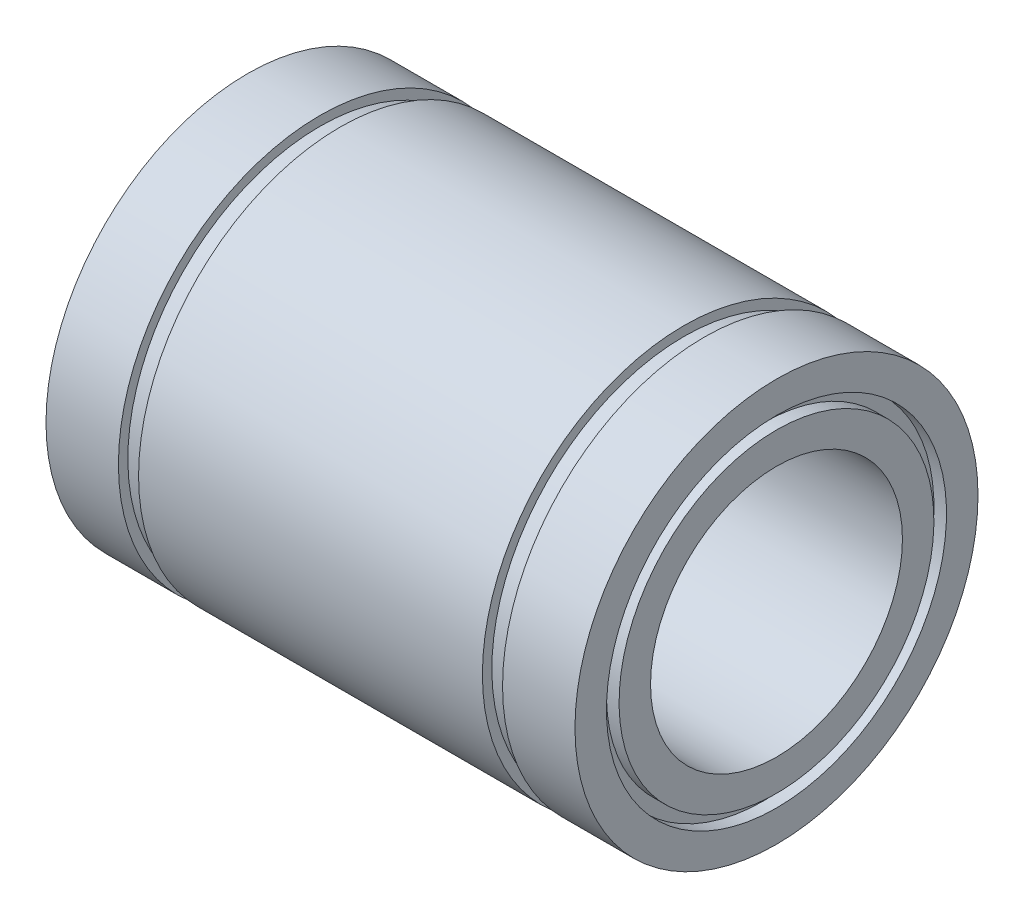
SolidWorks part; units mm, degrees
material "Ст3сп ГОСТ 535-2005"
ref_plane "Plano frontal" through (0, 0, 0) normal (0, 0, 1) x (1, 0, 0)
ref_plane "Plano superior" through (0, 0, 0) normal (0, 1, 0) x (1, 0, 0)
ref_plane "Plano direito" through (0, 0, 0) normal (1, 0, 0) x (0, 0, -1)
sketch "Esboço1" plane through (0, 0, 0) normal (0, 0, 1) x (1, 0, 0)
  line L0 (-21, 16) -> (-15.25, 16)
  line L1 (-15.25, 16) -> (-15.25, 15.25)
  line L2 (-15.25, 15.25) -> (-13.65, 15.25)
  line L3 (-13.65, 15.25) -> (-13.65, 16)
  line L4 (-13.65, 16) -> (13.65, 16)
  line L5 (13.65, 16) -> (13.65, 15.25)
  line L6 (13.65, 15.25) -> (15.25, 15.25)
  line L7 (15.25, 15.25) -> (15.25, 16)
  line L8 (15.25, 16) -> (21, 16)
  line L9 (21, 16) -> (21, 13.5)
  line L10 (21, 10) -> (-21, 10)
  line L11 (-21, 10) -> (-21, 12.5)
  line L12 (0, 10) -> (0, 0) construction
  line L13 (0, 0) -> (-86.5, 0) construction
  line L14 (-21, 13.5) -> (-21, 16)
  line L15 (-21, 13.5) -> (-20, 13.5)
  line L16 (21, 12.5) -> (21, 10)
  line L17 (-20, 13.5) -> (-20, 12.5)
  line L18 (-20, 12.5) -> (-21, 12.5)
  line L19 (21, 13.5) -> (20, 13.5)
  line L21 (21, 12.5) -> (20, 12.5)
  line L22 (20, 13.5) -> (20, 12.5)
  dimension "D1" = 42
  dimension "D2" = 30.5
  dimension "D3" = 1.6
  dimension "D4" = 20
  dimension "D5" = 32
  dimension "D6" = 30.5
  dimension "D7" = 1
  dimension "D8" = 1
  dimension "D9" = 1
  dimension "D10" = 1
revolve "Revolução1" add sketch "Esboço1" angle 360 about L13
